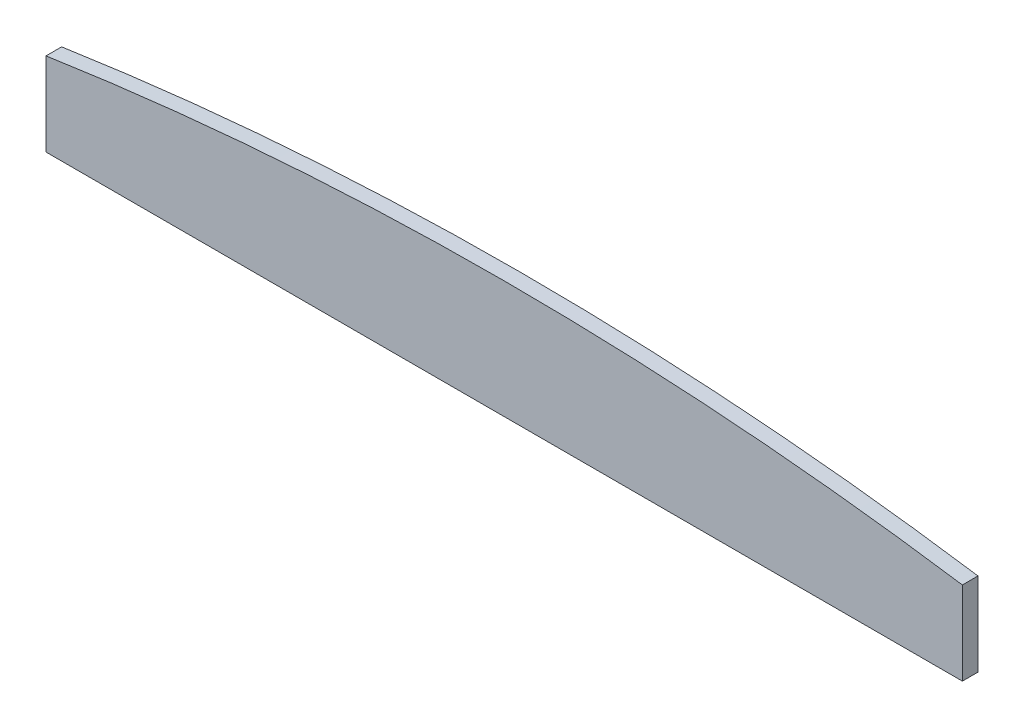
SolidWorks part; units mm, degrees
ref_plane "Front Plane" through (0, 0, 0) normal (0, 0, 1) x (1, 0, 0)
ref_plane "Top Plane" through (0, 0, 0) normal (0, 1, 0) x (1, 0, 0)
ref_plane "Right Plane" through (0, 0, 0) normal (1, 0, 0) x (0, 0, -1)
sketch "Sketch1" plane through (0, 0, 0) normal (0, 1, 0) x (1, 0, 0)
  line L1 (-58.7, 1) -> (58.7, 1)
  line L2 (-58.7, 1) -> (-58.7, -1)
  line L3 (-58.7, -1) -> (58.7, -1)
  line L4 (58.7, 1) -> (58.7, -1)
  line L5 (-58.7, 1) -> (58.7, -1) construction
  line L6 (-58.7, -1) -> (58.7, 1) construction
  point P0 (0, 0)
  dimension "D1" = 2
  dimension "D2" = 117.4
extrude "Boss-Extrude1" add sketch "Sketch1" along normal blind 16
sketch "Sketch2" plane through (0, 0, 1) normal (0, 0, 1) x (1, 0, 0)
  line L0 (-58.7, 16) -> (-58.7, 0) construction
  line L1 (58.7, 16) -> (58.7, 0) construction
  line L4 (-58.7, 10.6747) -> (-58.7, 16)
  line L5 (58.7, 10.6747) -> (58.7, 16)
  line L6 (-58.7, 16) -> (58.7, 16)
  arc A1 (-58.7, 10.6747) -> (58.7, 10.6747) centre (0, -379.677) cw
extrude "Cut-Extrude1" cut sketch "Sketch2" against normal blind 20
